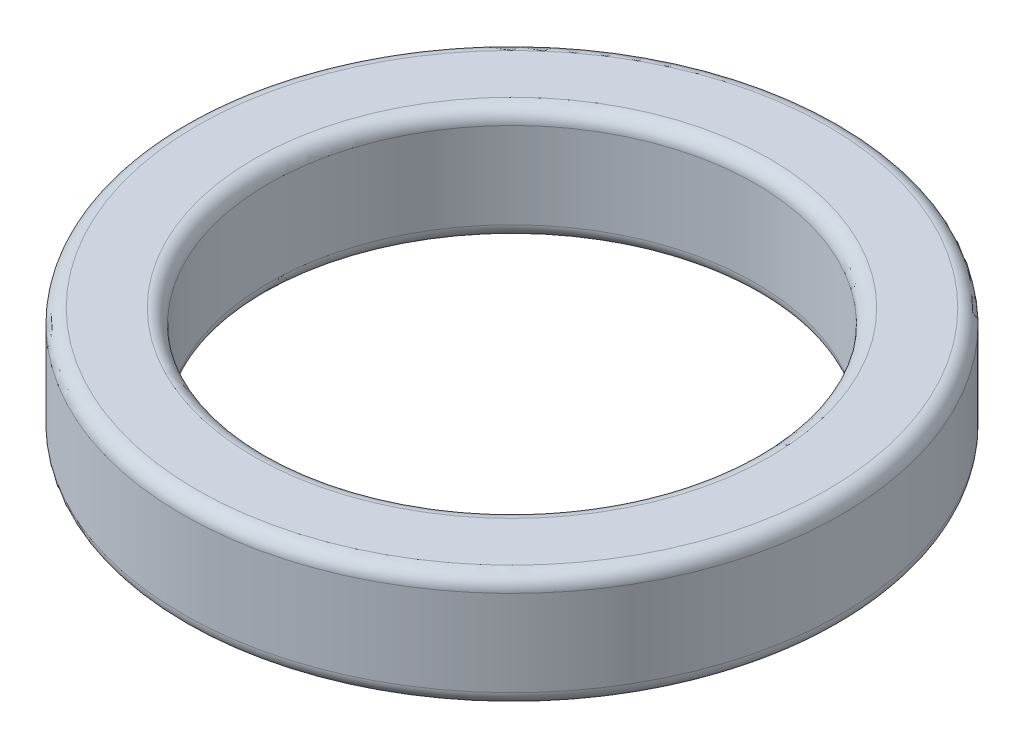
SolidWorks part; units mm, degrees
material "1023 Kohlenstoffstahlblech (SS)"
ref_plane "Ebene vorne" through (0, 0, 0) normal (0, 0, 1) x (1, 0, 0)
ref_plane "Ebene oben" through (0, 0, 0) normal (0, 1, 0) x (1, 0, 0)
ref_plane "Ebene rechts" through (0, 0, 0) normal (1, 0, 0) x (0, 0, -1)
sketch "Skizze1" plane through (0, 0, 0) normal (0, 1, 0) x (1, 0, 0)
  circle A0 centre (0, 0) radius 11.5
  circle A1 centre (0, 0) radius 8.5
  dimension "D1" = 23
  dimension "D2" = 17
extrude "Aufsatz-Linear austragen1" add sketch "Skizze1" along normal blind 4
fillet "Verrundung1" radius 0.5 4 edges at (0, 0, 11.5) (0, 0, 8.5) (0, 4, 8.5) (0, 4, 11.5)
